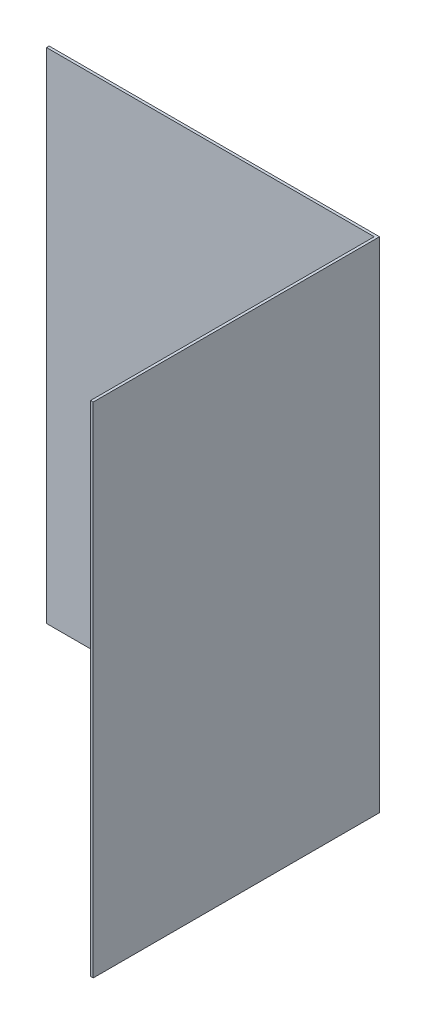
SolidWorks part; units mm, degrees
material "Copper"
ref_plane "Front Plane" through (0, 0, 0) normal (0, 0, 1) x (1, 0, 0)
ref_plane "Top Plane" through (0, 0, 0) normal (0, 1, 0) x (1, 0, 0)
ref_plane "Right Plane" through (0, 0, 0) normal (1, 0, 0) x (0, 0, -1)
sketch "Sketch1" plane through (0, 0, 0) normal (0, 0, 1) x (1, 0, 0)
  line L0 (15.875, 14.2939) -> (-15.875, 14.2939) construction
  line L1 (15.875, -14.4692) -> (-3.175, -14.4692)
  line L2 (15.875, -14.4692) -> (15.875, 14.2939)
  line L3 (15.875, 14.2939) -> (-3.175, 14.2939)
  line L4 (-3.175, -14.4692) -> (-3.175, 14.2939)
  line L5 (15.875, 38.1) -> (15.875, -38.1) construction
  circle A0 centre (9.525, 0) radius 1.5875 construction
  circle A1 centre (9.525, 0) radius 1.5875
  dimension "D1" = 19.05
extrude "Boss-Extrude1" add sketch "Sketch1" along normal blind 0.1524 contours L4 L3 L2 L1
sketch "Sketch2" plane through (0, 0, 0.1524) normal (0, 0, 1) x (1, 0, 0)
  line L0 (15.875, -14.4692) -> (-3.175, -14.4692) construction
  line L1 (15.875, 14.2939) -> (15.7226, 14.2939)
  line L2 (15.875, 14.2939) -> (15.875, -14.4692)
  line L3 (15.875, -14.4692) -> (15.7226, -14.4692)
  line L4 (15.7226, 14.2939) -> (15.7226, -14.4692)
  dimension ".006" = 0.1524
extrude "Boss-Extrude2" add sketch "Sketch2" along normal up to surface (16.3573 mm away)
